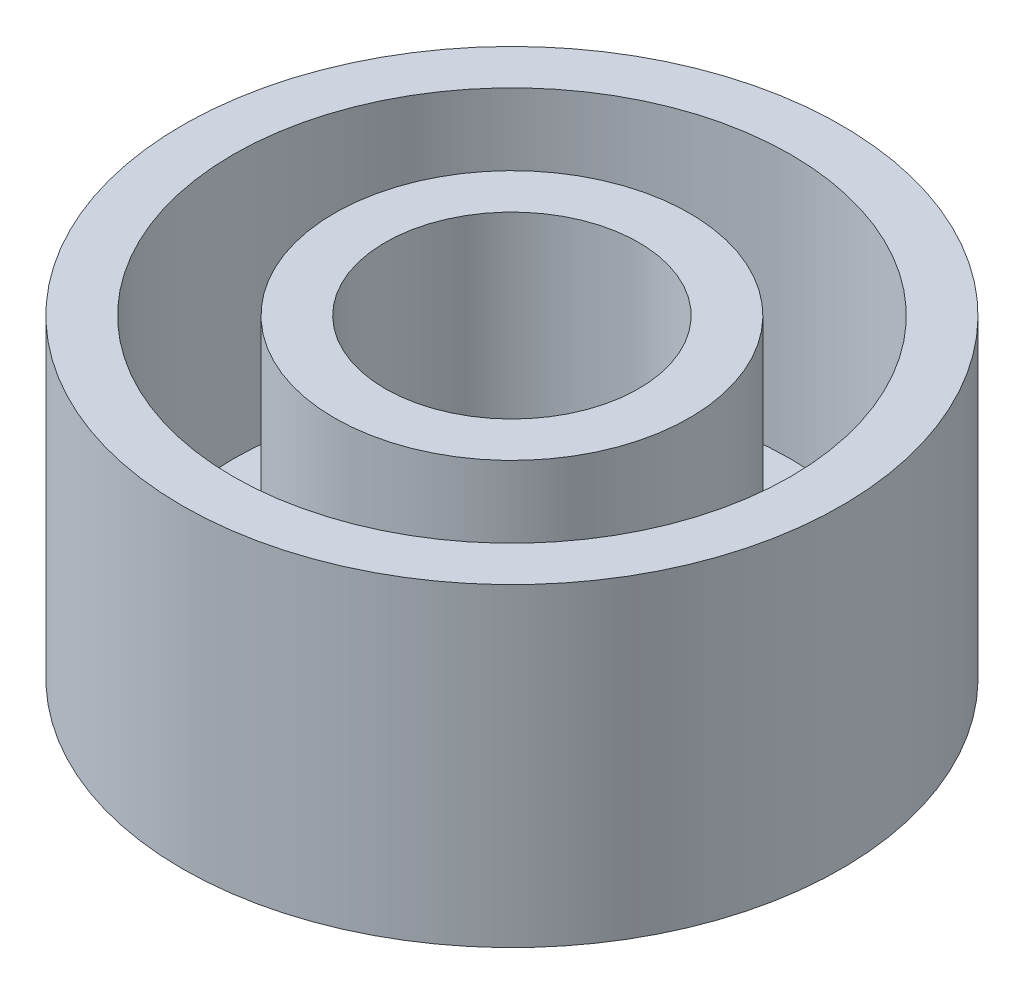
SolidWorks part; units mm, degrees
ref_plane "Front Plane" through (0, 0, 0) normal (0, 0, 1) x (1, 0, 0)
ref_plane "Top Plane" through (0, 0, 0) normal (0, 1, 0) x (1, 0, 0)
ref_plane "Right Plane" through (0, 0, 0) normal (1, 0, 0) x (0, 0, -1)
sketch "Sketch1" plane through (0, 0, 0) normal (0, 1, 0) x (1, 0, 0)
  line L0 (0, 0) -> (0, 20.0259) construction
  line L1 (0, 0) -> (29.0077, 0) construction
  circle A0 centre (0, 0) radius 27.5
  circle A1 centre (0, 0) radius 12.5
  circle A2 centre (0, 0) radius 8 construction
  circle A3 centre (0, 0) radius 32.5
  circle A4 centre (0, 0) radius 17.5
  dimension "D1" = 55
  dimension "D2" = 25
  dimension "D3" = 16
  dimension "D4" = 65
  dimension "D5" = 35
extrude "Boss-Extrude2" add sketch "Sketch1" along normal blind 26 contours A3 A0 | A4 A1
sketch "Sketch2" plane through (0, 0, 0) normal (0, 1, 0) x (1, 0, 0)
  circle A0 centre (0, 0) radius 32.5
  circle A2 centre (0, 0) radius 8
  dimension "D1" = 65
  dimension "D3" = 16
extrude "Boss-Extrude3" add sketch "Sketch2" against normal blind 5
sketch "Sketch3" plane through (0, 0, 0) normal (0, 1, 0) x (1, 0, 0)
  line L0 (0, 0) -> (0, 12.5) construction
  line L1 (0, 0) -> (-8.8388, 8.8388) construction
  line L2 (0, 0) -> (-8.8388, -8.8388) construction
  circle A1 centre (0, 0) radius 12.5 construction
  circle A2 centre (0, 0) radius 10.25 construction
  circle A3 centre (-7.2478, 7.2478) radius 1.5
  circle A4 centre (7.2478, 7.2478) radius 1.5
  circle A5 centre (7.2478, -7.2478) radius 1.5
  circle A6 centre (-7.2478, -7.2478) radius 1.5
  circle A7 centre (0, 0) radius 12.5 construction
  point P12 (0, 0)
  point P21 (0, 0)
  dimension "D2" = 20.5
  dimension "D3" = 3
  dimension "D1" = 45
  dimension "D5" = 45
  dimension "D4" = 4
extrude "Cut-Extrude1" cut sketch "Sketch3" along normal blind 3 and the other way through all
